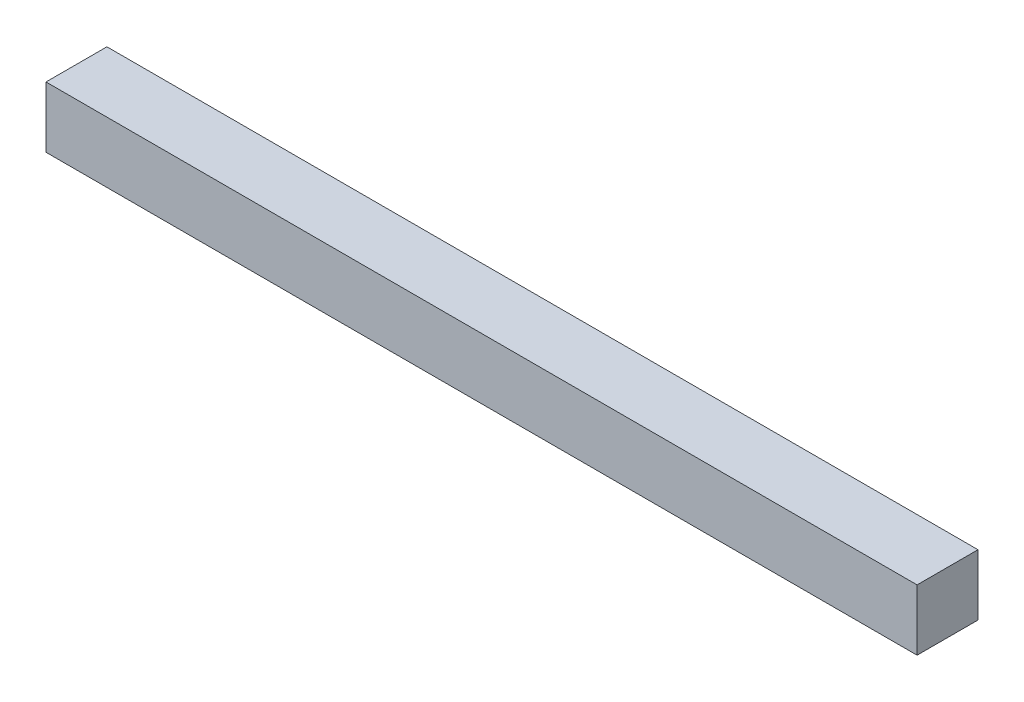
SolidWorks part; units mm, degrees
ref_plane "Plan de face" through (0, 0, 0) normal (0, 0, 1) x (1, 0, 0)
ref_plane "Plan de dessus" through (0, 0, 0) normal (0, 1, 0) x (1, 0, 0)
ref_plane "Plan de droite" through (0, 0, 0) normal (1, 0, 0) x (0, 0, -1)
sketch "Esquisse1" plane through (0, 0, 0) normal (0, 0, 1) x (1, 0, 0)
  line L1 (-5.3833, 3.1991) -> (137.6167, 3.1991)
  line L2 (-5.3833, 3.1991) -> (-5.3833, -6.8009)
  line L3 (-5.3833, -6.8009) -> (137.6167, -6.8009)
  line L4 (137.6167, 3.1991) -> (137.6167, -6.8009)
  dimension "D1" = 143
  dimension "D2" = 10
extrude "Boss.-Extru.1" add sketch "Esquisse1" along normal blind 10 contours L3 L4 L1 L2
equation "\"mm\"=10"
equation "\"D1@Esquisse1\"=\"LargeurBoite\" - \"LargeurGauche\" + 13"
equation "\"EpaisseurPlaque\"= 3"
equation "\"ProfondeurBoite\"=460"
equation "\"LongueurSyphon\"=270"
equation "\"LargeurSyphon\"=120"
equation "\"HauteurCoteDroit\"= 490"
equation "\"HauteurCoteGauche\"= 540"
equation "\"HauteurSolSyphon\"= 300"
equation "\"HauteurSyphon\"=\"HauteurCoteGauche\"-\"HauteurSolSyphon\""
equation "\"LargeurDroite\"=10"
equation "\"LargeurGauche\"=150"
equation "\"LargeurBoite\"= \"LargeurDroite\" + \"LargeurGauche\" + \"LargeurSyphon\""
